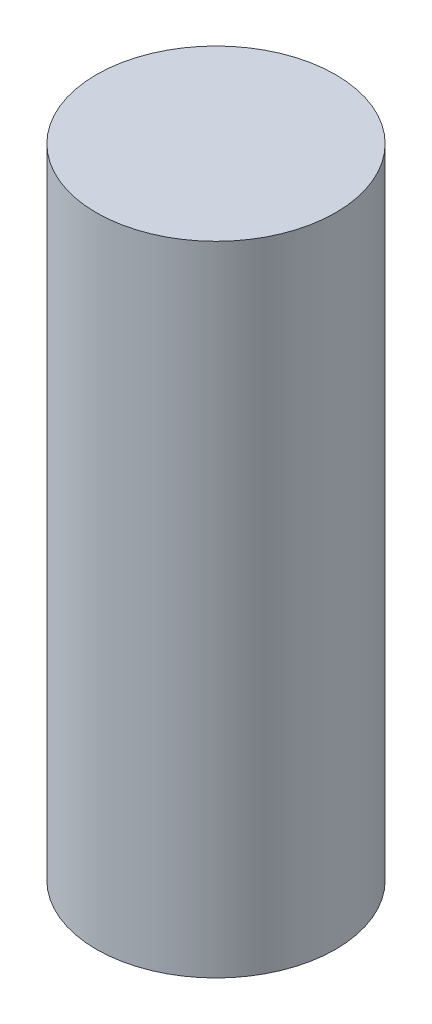
SolidWorks part; units mm, degrees
ref_plane "Front Plane" through (0, 0, 0) normal (0, 0, 1) x (1, 0, 0)
ref_plane "Top Plane" through (0, 0, 0) normal (0, 1, 0) x (1, 0, 0)
ref_plane "Right Plane" through (0, 0, 0) normal (1, 0, 0) x (0, 0, -1)
sketch "Sketch1" plane through (0, 0, 0) normal (0, 1, 0) x (1, 0, 0)
  circle A0 centre (0, 0) radius 38.1
  dimension "D1" = 76.2
extrude "Boss-Extrude1" add sketch "Sketch1" along normal blind 203.2
